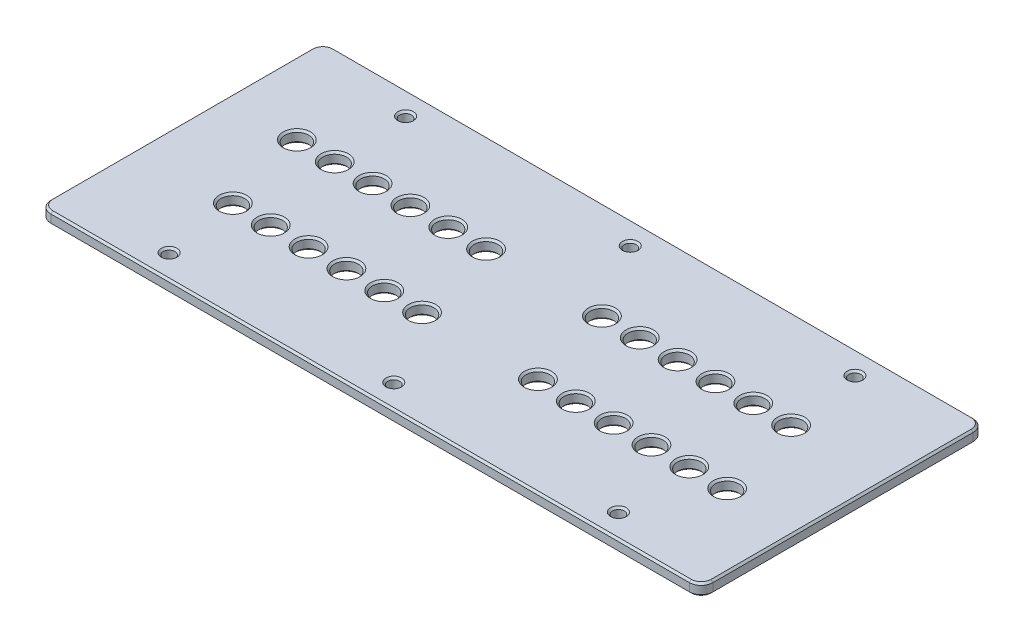
SolidWorks part; units mm, degrees
ref_plane "Front Plane" through (0, 0, 0) normal (0, 0, 1) x (1, 0, 0)
ref_plane "Top Plane" through (0, 0, 0) normal (0, 1, 0) x (1, 0, 0)
ref_plane "Right Plane" through (0, 0, 0) normal (1, 0, 0) x (0, 0, -1)
sketch "Sketch1" plane through (0, 0, 0) normal (0, 1, 0) x (1, 0, 0)
  line L1 (-88.9, -38.1) -> (88.9, -38.1)
  line L2 (-88.9, -38.1) -> (-88.9, 38.1)
  line L3 (-88.9, 38.1) -> (88.9, 38.1)
  line L4 (88.9, -38.1) -> (88.9, 38.1)
  line L5 (-88.9, -38.1) -> (88.9, 38.1) construction
  line L6 (-88.9, 38.1) -> (88.9, -38.1) construction
  point P0 (0, 0)
  dimension "D1" = 76.2
  dimension "D2" = 177.8
extrude "Boss-Extrude1" add sketch "Sketch1" along normal mid plane 3.175 contours L3 L4 L1 L2
hole_wizard "1/8 (0.125) Diameter Hole1" positions "Sketch2" profile "Sketch3" hole size "1/8" standard "ANSI Inch" end condition through all
sketch "Sketch2" plane through (0, 1.5875, 0) normal (0, 1, 0) x (1, 0, 0)
  line L0 (-60.325, -31.75) -> (-60.325, 31.75) construction
  line L1 (-60.325, 31.75) -> (0, 31.75) construction
  line L2 (0, 31.75) -> (60.325, 31.75) construction
  line L3 (60.325, 31.75) -> (60.325, -31.75) construction
  line L4 (60.325, -31.75) -> (0, -31.75) construction
  line L5 (0, -31.75) -> (-60.325, -31.75) construction
  line L7 (0, -31.75) -> (0, 31.75) construction
  line L9 (-60.325, 0) -> (-88.9, 0) construction
  line L10 (-88.9, -38.1) -> (-88.9, 38.1) construction
  line L12 (60.325, 0) -> (88.9, 0) construction
  line L13 (88.9, -38.1) -> (88.9, 38.1) construction
  line L14 (-88.9, 38.1) -> (88.9, 38.1) construction
  point P0 (-60.325, 31.75)
  point P2 (0, 31.75)
  point P4 (60.325, 31.75)
  point P6 (60.325, -31.75)
  point P8 (0, -31.75)
  point P10 (-60.325, -31.75)
  dimension "D1" = 28.575
  dimension "D2" = 6.35
sketch "Sketch3" plane through (-60.325, 1.5875, -31.75) normal (1, 0, 0) x (0, 0, 1)
  line L0 (0, 0) -> (0, 3.175)
  line L1 (0, 3.175) -> (1.5875, 3.175)
  line L2 (1.5875, 3.175) -> (1.5875, 0)
  line L5 (1.5875, 0) -> (0, 0)
  line L11 (0, -6.35) -> (0, 107.95) construction
  dimension "Thru Hole Dia." = 3.175
  dimension "Thru Hole Depth" = 3.175
hole_wizard "1/4 (0.25) Diameter Hole1" positions "Sketch4" profile "Sketch5" hole size "1/4" standard "ANSI Inch" end condition through all
sketch "Sketch4" plane through (0, 1.5875, 0) normal (0, 1, 0) x (1, 0, 0)
  line L0 (-88.9, -38.1) -> (88.9, -38.1) construction
  line L1 (-88.9, -38.1) -> (-88.9, 38.1) construction
  line L2 (-63.2866, -11.6611) -> (-53.1266, -11.6611) construction
  line L3 (-53.1266, -11.6611) -> (-42.9666, -11.6611) construction
  line L4 (-42.9666, -11.6611) -> (-32.8066, -11.6611) construction
  line L5 (-32.8066, -11.6611) -> (-22.6466, -11.6611) construction
  line L6 (-22.6466, -11.6611) -> (-12.4866, -11.6611) construction
  line L7 (18.6284, -11.6611) -> (28.7884, -11.6611) construction
  line L8 (28.7884, -11.6611) -> (38.9484, -11.6611) construction
  line L9 (38.9484, -11.6611) -> (49.1084, -11.6611) construction
  line L10 (49.1084, -11.6611) -> (59.2684, -11.6611) construction
  line L11 (59.2684, -11.6611) -> (69.4284, -11.6611) construction
  line L13 (-88.9, 38.1) -> (88.9, 38.1) construction
  line L14 (-69.4284, 11.6611) -> (-59.2684, 11.6611) construction
  line L15 (-59.2684, 11.6611) -> (-49.1084, 11.6611) construction
  line L16 (-49.1084, 11.6611) -> (-38.9484, 11.6611) construction
  line L17 (-38.9484, 11.6611) -> (-28.7884, 11.6611) construction
  line L18 (-28.7884, 11.6611) -> (-18.6284, 11.6611) construction
  line L19 (-18.6284, 11.6611) -> (12.4866, 11.6611) construction
  line L21 (22.6466, 11.6611) -> (32.8066, 11.6611) construction
  line L22 (32.8066, 11.6611) -> (42.9666, 11.6611) construction
  line L23 (42.9666, 11.6611) -> (53.1266, 11.6611) construction
  line L24 (53.1266, 11.6611) -> (63.2866, 11.6611) construction
  line L25 (63.2866, 11.6611) -> (53.1266, 11.6611) construction
  line L26 (-12.4866, -11.6611) -> (18.6284, -11.6611) construction
  line L28 (12.4866, 11.6611) -> (22.6466, 11.6611) construction
  point P0 (-63.2866, -11.6611)
  point P2 (-53.1266, -11.6611)
  point P4 (-42.9666, -11.6611)
  point P6 (-32.8066, -11.6611)
  point P8 (-22.6466, -11.6611)
  point P10 (-12.4866, -11.6611)
  point P12 (18.6284, -11.6611)
  point P14 (28.7884, -11.6611)
  point P16 (38.9484, -11.6611)
  point P18 (49.1084, -11.6611)
  point P20 (59.2684, -11.6611)
  point P22 (69.4284, -11.6611)
  point P24 (-69.4284, 11.6611)
  point P26 (-59.2684, 11.6611)
  point P28 (-49.1084, 11.6611)
  point P30 (-38.9484, 11.6611)
  point P32 (-28.7884, 11.6611)
  point P34 (-18.6284, 11.6611)
  point P36 (12.4866, 11.6611)
  point P38 (22.6466, 11.6611)
  point P40 (32.8066, 11.6611)
  point P42 (42.9666, 11.6611)
  point P44 (53.1266, 11.6611)
  point P46 (63.2866, 11.6611)
  point P48 (53.1266, 11.6611)
  dimension "D1" = 26.4389
  dimension "D2" = 25.6134
  dimension "D3" = 10.16
  dimension "D4" = 31.115
  dimension "D5" = 19.4716
  dimension "D6" = 26.4389
sketch "Sketch5" plane through (-63.2866, 1.5875, 11.6611) normal (1, 0, 0) x (0, 0, 1)
  line L0 (0, 0) -> (0, 3.175)
  line L1 (0, 3.175) -> (3.175, 3.175)
  line L2 (3.175, 3.175) -> (3.175, 0)
  line L5 (3.175, 0) -> (0, 0)
  line L11 (0, -6.35) -> (0, 107.95) construction
  dimension "Thru Hole Dia." = 6.35
  dimension "Thru Hole Depth" = 3.175
fillet "Fillet1" radius 3.175 4 edges at (-88.9, 0, -38.1) (88.9, 0, -38.1) (88.9, 0, 38.1) (-88.9, 0, 38.1)
chamfer "Chamfer1" distance 0.508 angle 45 76 edges at (60.325, -1.5875, 33.3375) (0, -1.5875, 33.3375) (-60.325, -1.5875, 33.3375) (-87.9701, -1.5875, 37.1701) (0, -1.5875, 38.1) (87.9701, -1.5875, 37.1701) (88.9, -1.5875, 0) (87.9701, -1.5875, -37.1701) (0, -1.5875, -38.1) (-87.9701, -1.5875, -37.1701) (-88.9, -1.5875, 0) (60.325, -1.5875, -30.1625) (0, -1.5875, -30.1625) (-60.325, -1.5875, -30.1625) (-60.325, 1.5875, -30.1625) (87.9701, 1.5875, -37.1701) (88.9, 1.5875, 0) (87.9701, 1.5875, 37.1701) (0, 1.5875, 38.1) (-87.9701, 1.5875, 37.1701) (-88.9, 1.5875, 0) (-87.9701, 1.5875, -37.1701) (0, 1.5875, -38.1) (-60.325, 1.5875, 33.3375) (0, 1.5875, 33.3375) (60.325, 1.5875, 33.3375) (60.325, 1.5875, -30.1625) (0, 1.5875, -30.1625) (59.2684, -1.5875, 14.8361) (69.4284, -1.5875, 14.8361) (-69.4284, -1.5875, -8.4861) (-59.2684, -1.5875, -8.4861) (-49.1084, -1.5875, -8.4861) (-38.9484, -1.5875, -8.4861) (-28.7884, -1.5875, -8.4861) (-18.6284, -1.5875, -8.4861) (12.4866, -1.5875, -8.4861) (22.6466, -1.5875, -8.4861) (32.8066, -1.5875, -8.4861) (53.1266, -1.5875, -8.4861) (63.2866, -1.5875, -8.4861) (42.9666, -1.5875, -8.4861) (49.1084, -1.5875, 14.8361) (38.9484, -1.5875, 14.8361) (28.7884, -1.5875, 14.8361) (18.6284, -1.5875, 14.8361) (-12.4866, -1.5875, 14.8361) (-22.6466, -1.5875, 14.8361) (-32.8066, -1.5875, 14.8361) (-42.9666, -1.5875, 14.8361) (-53.1266, -1.5875, 14.8361) (-63.2866, -1.5875, 14.8361) (-63.2866, 1.5875, 14.8361) (-38.9484, 1.5875, -8.4861) (53.1266, 1.5875, -8.4861) (63.2866, 1.5875, -8.4861) (42.9666, 1.5875, -8.4861) (32.8066, 1.5875, -8.4861) (22.6466, 1.5875, -8.4861) (12.4866, 1.5875, -8.4861) (-18.6284, 1.5875, -8.4861) (-28.7884, 1.5875, -8.4861) (-49.1084, 1.5875, -8.4861) (-59.2684, 1.5875, -8.4861) (-69.4284, 1.5875, -8.4861) (69.4284, 1.5875, 14.8361) (59.2684, 1.5875, 14.8361) (49.1084, 1.5875, 14.8361) (38.9484, 1.5875, 14.8361) (28.7884, 1.5875, 14.8361) (18.6284, 1.5875, 14.8361) (-12.4866, 1.5875, 14.8361) (-22.6466, 1.5875, 14.8361) (-32.8066, 1.5875, 14.8361) (-42.9666, 1.5875, 14.8361) (-53.1266, 1.5875, 14.8361)
